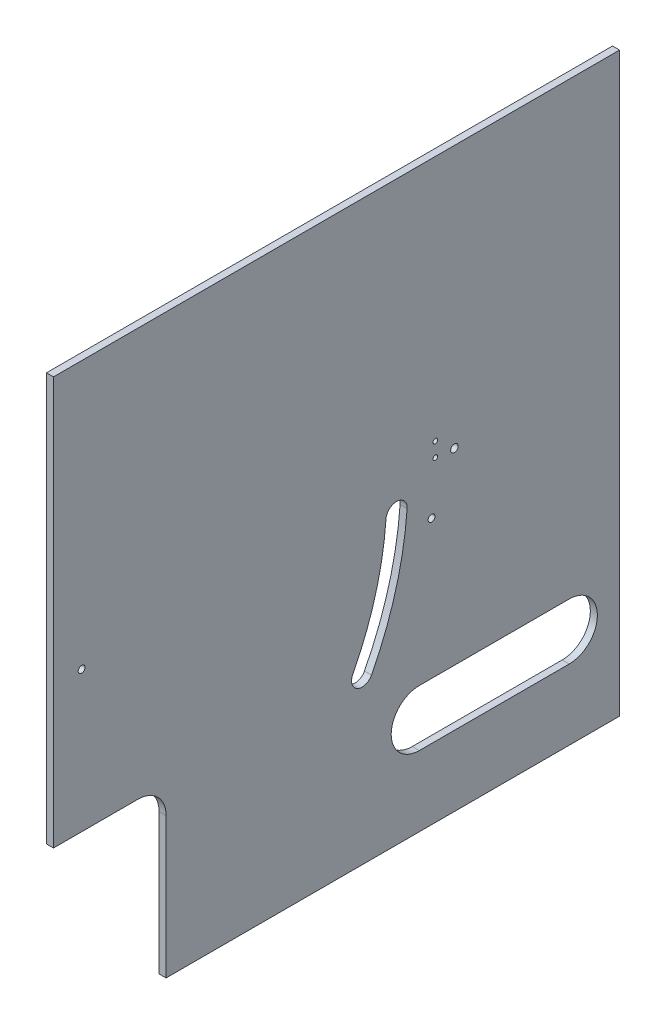
SolidWorks part; units mm, degrees
material "Acrylic (Medium-high impact)"
ref_plane "Front" through (0, 0, 0) normal (0, 0, 1) x (1, 0, 0)
ref_plane "Top" through (0, 0, 0) normal (0, 1, 0) x (1, 0, 0)
ref_plane "Right" through (0, 0, 0) normal (1, 0, 0) x (0, 0, -1)
sketch "Sketch1" plane through (0, 0, 0) normal (1, 0, 0) x (0, 0, -1)
  line L1 (-127.725, 130.175) -> (127.725, 130.175)
  line L2 (-127.725, 130.175) -> (-127.725, -130.175)
  line L3 (-127.725, -130.175) -> (127.725, -130.175)
  line L4 (127.725, 130.175) -> (127.725, -130.175)
  point P4 (-127.725, 0)
  point P6 (0, 130.175)
  dimension "D1" = 260.35
  dimension "D2" = 255.45
extrude "Boss-Extrude1" add sketch "Sketch1" along normal blind 3.175
sketch "Sketch2" plane through (3.175, 0, 0) normal (1, 0, 0) x (0, 0, -1)
  line L0 (127.725, -130.175) -> (127.725, 130.175) construction
  line L1 (-127.725, 130.175) -> (127.725, 130.175)
  line L2 (-127.725, 130.175) -> (-127.725, 123.825)
  line L3 (-127.725, 123.825) -> (127.725, 123.825)
  line L4 (127.725, 130.175) -> (127.725, 123.825)
  dimension "D1" = 6.35
extrude "Boss-Extrude2" add sketch "Sketch2" along normal blind 12.7
sketch "Sketch3" plane through (0, 0, 0) normal (-1, 0, 0) x (0, 0, 1)
  line L0 (-105.025, -73.025) -> (-37.375, -73.025)
  line L1 (-37.375, -98.425) -> (-105.025, -98.425)
  line L2 (0.725, 130.175) -> (0.725, -130.175) construction
  line L3 (-127.725, 130.175) -> (127.725, 130.175) construction
  line L4 (127.725, -130.175) -> (-127.725, -130.175) construction
  line L5 (127.725, 130.175) -> (127.725, -130.175) construction
  arc A0 (-37.375, -73.025) -> (-37.375, -98.425) centre (-37.375, -85.725) cw
  arc A1 (-105.025, -98.425) -> (-105.025, -73.025) centre (-105.025, -85.725) cw
  dimension "D1" = 25.4
  dimension "D3" = 232.75
  dimension "D2" = 38.1
  dimension "D4" = 127
  dimension "D5" = 44.45
extrude "Cut-Extrude1" cut sketch "Sketch3" against normal through all
sketch "Sketch5" plane through (0, 0, -127.725) normal (0, 0, -1) x (-1, 0, 0)
  line L1 (-3.175, 123.825) -> (-57.7651, 123.825)
  line L2 (-3.175, 123.825) -> (-3.175, 157.6842)
  line L3 (-3.175, 157.6842) -> (-57.7651, 157.6842)
  line L4 (-57.7651, 123.825) -> (-57.7651, 157.6842)
extrude "Cut-Extrude2" cut sketch "Sketch5" against normal through all
sketch "Sketch6" plane through (3.175, 0, 0) normal (1, 0, 0) x (0, 0, -1)
  line L0 (89.875, -88.265) -> (89.875, -83.185)
  line L1 (111.875, -83.185) -> (111.875, -88.265)
  line L2 (83.875, -103.765) -> (83.875, -98.685)
  line L3 (86.875, -103.765) -> (86.875, -98.685)
  line L4 (83.875, -72.765) -> (83.875, -67.685)
  line L5 (86.875, -72.765) -> (86.875, -67.685)
  line L6 (100.875, -83.185) -> (100.875, -88.265) construction
  line L7 (117.875, -103.765) -> (117.875, -98.685)
  line L8 (114.875, -103.765) -> (114.875, -98.685)
  line L9 (114.875, -72.765) -> (114.875, -67.685)
  line L10 (117.875, -72.765) -> (117.875, -67.685)
  line L11 (-127.725, 130.175) -> (-127.725, -130.175) construction
  line L12 (-127.725, -130.175) -> (127.725, -130.175) construction
  arc A0 (89.875, -88.265) -> (111.875, -88.265) centre (100.875, -88.265) ccw
  arc A1 (111.875, -83.185) -> (89.875, -83.185) centre (100.875, -83.185) ccw
  arc A2 (83.875, -103.765) -> (86.875, -103.765) centre (85.375, -103.765) ccw
  arc A3 (86.875, -98.685) -> (83.875, -98.685) centre (85.375, -98.685) ccw
  arc A4 (83.875, -72.765) -> (86.875, -72.765) centre (85.375, -72.765) ccw
  arc A5 (86.875, -67.685) -> (83.875, -67.685) centre (85.375, -67.685) ccw
  arc A6 (117.875, -103.765) -> (114.875, -103.765) centre (116.375, -103.765) cw
  arc A7 (114.875, -98.685) -> (117.875, -98.685) centre (116.375, -98.685) cw
  arc A8 (117.875, -72.765) -> (114.875, -72.765) centre (116.375, -72.765) cw
  arc A9 (114.875, -67.685) -> (117.875, -67.685) centre (116.375, -67.685) cw
  circle A10 centre (85.375, -69.36) radius 3.175
  circle A11 centre (116.375, -69.36) radius 3.175
  circle A12 centre (85.375, -102.09) radius 3.175
  circle A13 centre (116.375, -102.09) radius 3.175
  point P37 (100.875, -85.725)
  point P38 (111.875, -85.725)
  dimension "D5" = 1.5
  dimension "D9" = 1.5
  dimension "D12" = 6.35
  dimension "D1" = 5.08
  dimension "D2" = 5.08
  dimension "D3" = 15.5
  dimension "D4" = 15.5
  dimension "D6" = 15.5
  dimension "D7" = 15.5
  dimension "D8" = 5.08
  dimension "D10" = 228.6
  dimension "D11" = 44.45
extrude "Cut-Extrude5" [suppressed] cut sketch "Sketch6" against normal through all contours L5 A10 A5 | L4 A10 L5 A5 | A5 A10 L4 | L9 A11 L10 A9 | A9 A11 L9 | L10 A11 A9 | A2 A12 L3 | L3 A12 L2 A2 | L2 A12 A2 | L7 A13 L8 A6 | A6 A13 L7 | L8 A13 A6
sketch "Sketch7" plane through (3.175, 0, 0) normal (1, 0, 0) x (0, 0, -1)
  line L0 (-127.725, 130.175) -> (-127.725, -130.175) construction
  line L1 (-127.725, -123.825) -> (127.725, -123.825)
  line L2 (-127.725, -123.825) -> (-127.725, -130.175)
  line L3 (-127.725, -130.175) -> (127.725, -130.175)
  line L4 (127.725, -123.825) -> (127.725, -130.175)
  line L5 (-127.725, -130.175) -> (127.725, -130.175) construction
  line L6 (127.725, -130.175) -> (127.725, 130.175) construction
  dimension "D1" = 6.35
extrude "Cut-Extrude6" [suppressed] cut sketch "Sketch7" against normal through all
sketch "Sketch8" plane through (0, 0, 0) normal (-1, 0, 0) x (0, 0, 1)
  line L0 (127.725, 130.175) -> (127.725, -130.175) construction
  line L1 (127.725, -130.175) -> (-127.725, -130.175) construction
  line L3 (127.725, -130.175) -> (-127.725, -130.175) construction
  circle A0 centre (115.025, 9.525) radius 1.55
  circle A3 centre (-53.205, 11.825) radius 1.7
  circle A4 centre (-42.905, -10.375) radius 1.55
  circle A5 centre (-44.605, 18.925) radius 1.05
  circle A6 centre (-44.605, 12.425) radius 1.05
  point P11 (-36.105, 22.225)
  dimension "D1" = 3.1
  dimension "D4" = 10.3
  dimension "D5" = 17.1
  dimension "D10" = 3.1
  dimension "D11" = 3.4
  dimension "D14" = 22.2
  dimension "D15" = 3.3
  dimension "D8" = 2.1
  dimension "D2" = 12.7
  dimension "D3" = 139.7
  dimension "D6" = 151.13
  dimension "D7" = 152.4
  dimension "D9" = 6.5
  dimension "D12" = 8.5
  dimension "D13" = 32.6
extrude "Cut-Extrude7" cut sketch "Sketch8" against normal through all
sketch "Sketch9" plane through (0, 0, 0) normal (-1, 0, 0) x (0, 0, 1)
  line L0 (127.725, 130.175) -> (127.725, -130.175) construction
  line L1 (127.725, -53.975) -> (76.925, -53.975)
  line L2 (127.725, -53.975) -> (127.725, -130.175)
  line L3 (127.725, -130.175) -> (76.925, -130.175)
  line L4 (76.925, -53.975) -> (76.925, -130.175)
  line L5 (127.725, -130.175) -> (-127.725, -130.175) construction
  dimension "D1" = 50.8
  dimension "D2" = 76.2
extrude "Cut-Extrude8" cut sketch "Sketch9" against normal through all
fillet "Fillet1" radius 12.7 1 edges at (1.5875, -53.975, 76.925)
sketch "Sketch10" plane through (0, 0, 0) normal (-1, 0, 0) x (0, 0, 1)
  line L3 (-31.867, -1.0885) -> (-22.342, -0.4003) construction
  line L4 (-9.3573, -130.175) -> (-9.3573, -60.175) construction
  line L5 (76.925, -130.175) -> (-127.725, -130.175) construction
  line L6 (-15.792, -58.1271) -> (-7.3094, -53.7403) construction
  arc A2 (-15.792, -58.1271) -> (-7.3094, -53.7403) centre (-11.5507, -55.9337) ccw
  arc A4 (-31.867, -1.0885) -> (-15.792, -58.1271) centre (115.025, 9.525) ccw
  arc A5 (-22.342, -0.4003) -> (-7.3094, -53.7403) centre (115.025, 9.525) ccw
  arc A7 (-22.342, -0.4003) -> (-31.867, -1.0885) centre (-27.1045, -0.7444) ccw
  circle A8 centre (115.025, 9.525) radius 142.5 construction
  point P24 (-9.3573, -60.175)
  dimension "D1" = 285
  dimension "D2" = 9.525
  dimension "D3" = 53.34
  dimension "D5" = 70
extrude "Cut-Extrude9" cut sketch "Sketch10" against normal through all
equation "\"bottomThickness\"= .25in"
equation "\"wallThickness\"= .125in"
equation "\"D1@Boss-Extrude1\"=\"wallThickness\""
